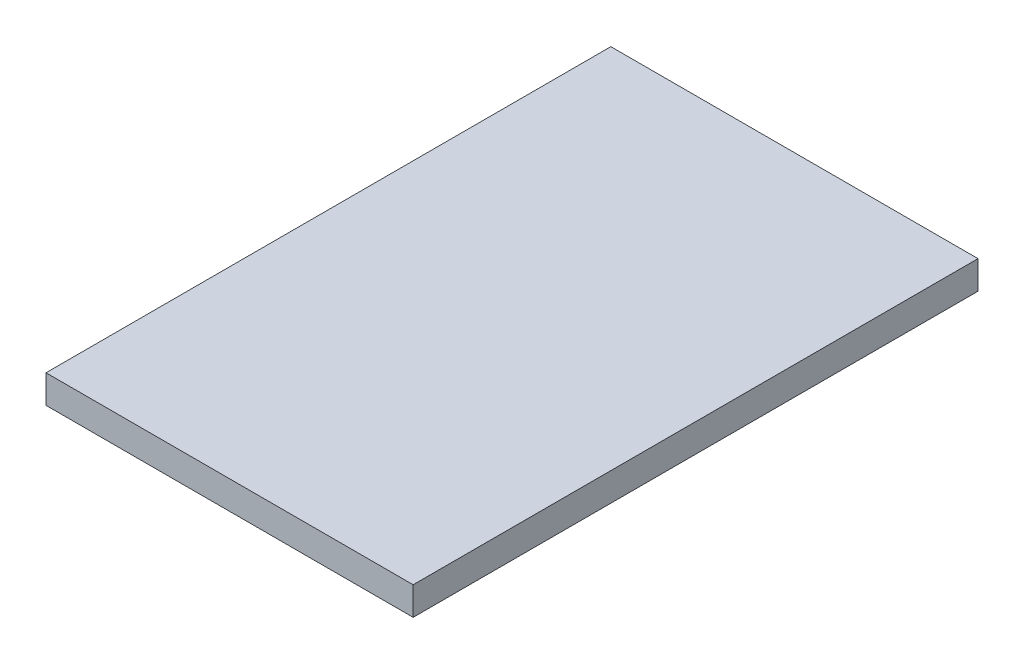
SolidWorks part; units mm, degrees
ref_plane "Front Plane" through (0, 0, 0) normal (0, 0, 1) x (1, 0, 0)
ref_plane "Top Plane" through (0, 0, 0) normal (0, 1, 0) x (1, 0, 0)
ref_plane "Right Plane" through (0, 0, 0) normal (1, 0, 0) x (0, 0, -1)
sketch "Sketch1" plane through (0, 0, 0) normal (0, 1, 0) x (1, 0, 0)
  line L1 (-106.569, 229.7043) -> (223.631, 229.7043)
  line L2 (-106.569, 229.7043) -> (-106.569, -278.2957)
  line L3 (-106.569, -278.2957) -> (223.631, -278.2957)
  line L4 (223.631, 229.7043) -> (223.631, -278.2957)
  dimension "D1" = 508
  dimension "D2" = 330.2
extrude "Boss-Extrude1" add sketch "Sketch1" along normal blind 25.4
